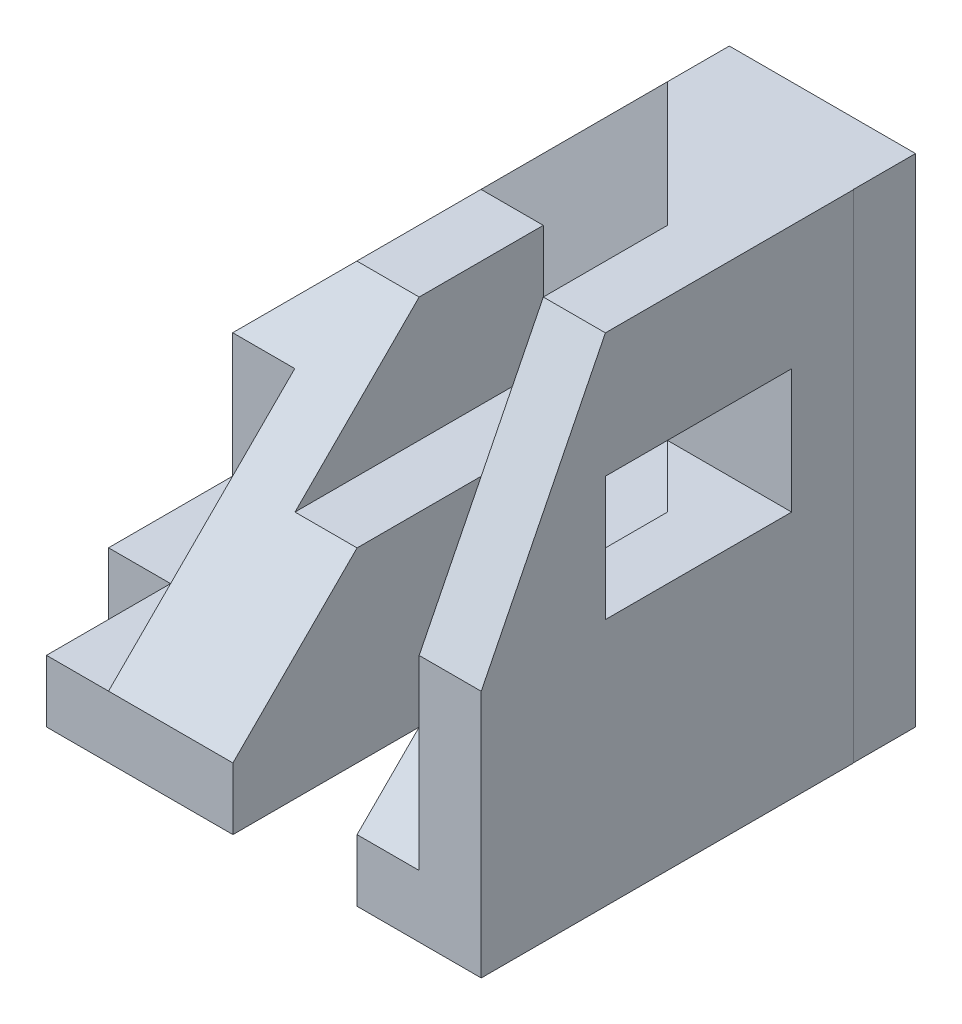
SolidWorks part; units mm, degrees
ref_plane "Front Plane" through (0, 0, 0) normal (0, 0, 1) x (1, 0, 0)
ref_plane "Top Plane" through (0, 0, 0) normal (0, 1, 0) x (1, 0, 0)
ref_plane "Right Plane" through (0, 0, 0) normal (1, 0, 0) x (0, 0, -1)
sketch "Sketch2" plane through (0, 0, 0) normal (0, 0, 1) x (1, 0, 0)
  line L0 (0, 0) -> (0, 3)
  line L1 (0, 3) -> (5, 8)
  line L2 (5, 8) -> (8, 8)
  line L3 (8, 8) -> (8, 0)
  line L4 (8, 0) -> (0, 0)
  dimension "D1" = 3
  dimension "D2" = 5
  dimension "D3" = 5
  dimension "D4" = 8
extrude "Boss-Extrude1" add sketch "Sketch2" along normal blind 1
sketch "Sketch3" plane through (0, 0, 1) normal (0, 0, 1) x (1, 0, 0)
  line L0 (0, 0) -> (0, 3)
  line L1 (0, 3) -> (2, 5)
  line L2 (5, 8) -> (0, 3) construction
  line L3 (2, 5) -> (3.0038, 5)
  line L4 (3.0038, 5) -> (3.0038, 3)
  line L5 (3.0038, 3) -> (3.0038, 0)
  line L6 (0, 0) -> (8, 0) construction
  line L7 (3.0038, 0) -> (0, 0)
  dimension "D1" = 2
extrude "Boss-Extrude2" add sketch "Sketch3" along normal blind 6
sketch "Sketch4" plane through (0, 0, 0) normal (-1, 0, 0) x (0, 0, 1)
  line L0 (7, 5) -> (1, 5) construction
  line L1 (3, 5) -> (7, 1)
  line L2 (7, 3) -> (7, 0) construction
  line L3 (7, 1) -> (7, 5)
  line L4 (7, 5) -> (3, 5)
  point P0 (3, 5)
  dimension "D1" = 2
  dimension "D2" = 1
extrude "Cut-Extrude1" cut sketch "Sketch4" against normal blind 4
sketch "Sketch5" plane through (0, 5, 0) normal (0, 1, 0) x (1, 0, 0)
  line L1 (0, -5) -> (2, -3) construction
  line L3 (1, -4) -> (1, -3)
  line L4 (1, -3) -> (0, -3)
  line L6 (0, -5) -> (0, 0) construction
  line L7 (0, -3) -> (0, -3.75)
  line L8 (0, -3.75) -> (0, -7)
  line L9 (0, -7) -> (2, -7)
  line L10 (3.0038, -7) -> (0, -7) construction
  line L11 (2, -7) -> (2, -4)
  line L12 (2, -4) -> (1, -4)
  point P0 (1, -4)
  point P1 (2, -3)
  dimension "D1" = 1
extrude "Cut-Extrude2" cut sketch "Sketch5" against normal blind 4
sketch "Sketch6" plane through (0, 1, 0) normal (0, 1, 0) x (1, 0, 0)
  line L0 (1, -7) -> (1, -5)
  line L1 (0, -7) -> (2, -7) construction
  line L2 (1, -5) -> (0, -5)
  line L3 (0, -3) -> (0, -7) construction
  line L4 (0, -5) -> (0, -7)
  line L5 (0, -7) -> (1, -7)
  dimension "D1" = 2
  dimension "D2" = 1
extrude "Cut-Extrude3" cut sketch "Sketch6" against normal blind 4
sketch "Sketch7" plane through (3.0038, 0, 0) normal (1, 0, 0) x (0, 0, -1)
  line L0 (-7, 0) -> (-7, 1)
  line L1 (-7, 1) -> (-4, 4)
  line L2 (-3, 5) -> (-7, 1) construction
  line L3 (-4, 4) -> (-1, 4)
  line L4 (-1, 0) -> (-1, 5) construction
  line L5 (-1, 4) -> (-1, 0)
  line L6 (-1, 0) -> (-7, 0)
  line L7 (-3, 5) -> (-1, 5) construction
  dimension "D1" = 1
extrude "Boss-Extrude3" add sketch "Sketch7" along normal blind 4
sketch "Sketch8" plane through (0, 4, 0) normal (0, 1, 0) x (1, 0, 0)
  line L0 (7.0038, -7) -> (2, -7) construction
  line L1 (4.0038, -3) -> (6.0038, -3)
  line L2 (4.0038, -3) -> (4.0038, -7)
  line L3 (4.0038, -7) -> (6.0038, -7)
  line L4 (6.0038, -3) -> (6.0038, -7)
  line L5 (3.0038, -1) -> (3.0038, -4) construction
  dimension "D1" = 4
  dimension "D2" = 2
  dimension "D3" = 1
extrude "Cut-Extrude4" cut sketch "Sketch8" against normal blind 4
sketch "Sketch9" plane through (7.0038, 0, 0) normal (1, 0, 0) x (0, 0, -1)
  line L0 (-1, 0) -> (-1, 8) construction
  line L1 (-7, 0) -> (-1, 0)
  line L2 (-7, 0) -> (-7, 4)
  line L3 (-5, 8) -> (-1, 8)
  line L4 (-1, 0) -> (-1, 8)
  line L5 (-7, 4) -> (-5, 8)
  point P2 (-7, 8)
  dimension "D1" = 4
  dimension "D2" = 2
extrude "Boss-Extrude4" add sketch "Sketch9" along normal blind 1
sketch "Sketch14" plane through (3.0038, 0, 0) normal (1, 0, 0) x (0, 0, -1)
  line L1 (-1, 4) -> (-5.503, 4)
  line L2 (-1, 4) -> (-1, 3)
  line L3 (-1, 3) -> (-5.503, 3)
  line L4 (-5.503, 4) -> (-5.503, 3)
  dimension "D1" = 1
extrude "Cut-Extrude6" cut sketch "Sketch14" along normal blind 4
sketch "Sketch11" plane through (8.0038, 0, 0) normal (1, 0, 0) x (0, 0, -1)
  line L0 (-1, 8) -> (-5, 8) construction
  line L1 (-5, 4) -> (-2, 4)
  line L2 (-5, 4) -> (-5, 6)
  line L3 (-5, 6) -> (-2, 6)
  line L4 (-2, 4) -> (-2, 6)
  line L5 (-7, 4) -> (-7, 0) construction
  dimension "D1" = 3
  dimension "D2" = 2
  dimension "D3" = 2
  dimension "D4" = 2
extrude "Cut-Extrude5" cut sketch "Sketch11" against normal blind 2
sketch "Sketch15" plane through (0, 3, 0) normal (0, 1, 0) x (1, 0, 0)
  line L0 (7.0038, -3) -> (5.0038, -1)
  line L1 (7.0038, -5) -> (7.0038, -1) construction
  line L2 (7.0038, -1) -> (3.0038, -1) construction
  line L3 (5.0038, -1) -> (7.0038, -1)
  line L4 (7.0038, -1) -> (7.0038, -3)
  dimension "D1" = 2
  dimension "D2" = 2
extrude "Boss-Extrude5" add sketch "Sketch15" along normal blind 5
sketch "Sketch16" plane through (7.0038, 0, 0) normal (1, 0, 0) x (0, 0, -1)
  line L1 (-3, 6) -> (-2, 6)
  line L2 (-3, 6) -> (-3, 4)
  line L3 (-3, 4) -> (-2, 4)
  line L4 (-2, 6) -> (-2, 4)
extrude "Cut-Extrude7" cut sketch "Sketch16" against normal blind 3
